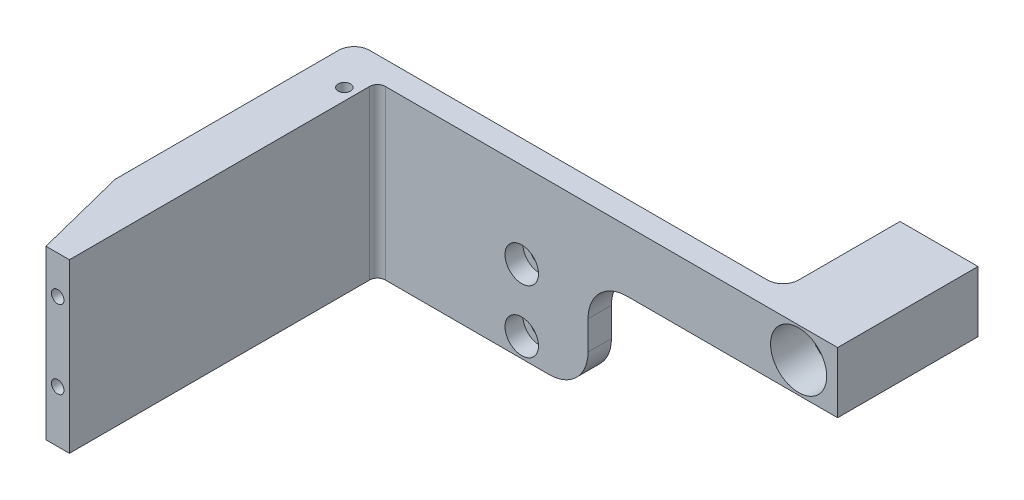
SolidWorks part; units mm, degrees
ref_plane "前视基准面" through (0, 0, 0) normal (0, 0, 1) x (1, 0, 0)
ref_plane "上视基准面" through (0, 0, 0) normal (0, 1, 0) x (1, 0, 0)
ref_plane "右视基准面" through (0, 0, 0) normal (1, 0, 0) x (0, 0, -1)
sketch "草图1" plane through (0, 0, 0) normal (0, 0, 1) x (1, 0, 0)
  line L1 (20, -5) -> (-20, -5)
  line L2 (20, -5) -> (20, 5)
  line L3 (20, 5) -> (-20, 5)
  line L4 (-20, -5) -> (-20, 5)
  line L5 (20, -5) -> (-20, 5) construction
  line L6 (20, 5) -> (-20, -5) construction
  point P0 (0, 0)
  dimension "D1" = 40
  dimension "D2" = 10
extrude "凸台-拉伸1" add sketch "草图1" along normal blind 3
sketch "草图2" plane through (0, 0, 3) normal (0, 0, 1) x (1, 0, 0)
  line L0 (-10, 5) -> (-10, -5)
  line L1 (20, 5) -> (-20, 5) construction
  line L2 (-20, -5) -> (20, -5) construction
  line L3 (-10, -5) -> (-7, -5)
  line L4 (-7, -5) -> (-7, 5)
  line L5 (-7, 5) -> (-10, 5)
  line L6 (-20, 5) -> (-20, -5) construction
  dimension "D1" = 3
  dimension "D2" = 10
extrude "凸台-拉伸2" add sketch "草图2" along normal blind 39.5
sketch "草图3" plane through (0, 5, 0) normal (0, 1, 0) x (1, 0, 0)
  line L0 (-20, -3) -> (-10, -42.5)
  line L1 (-10, -42.5) -> (-10, -30.2762)
  line L2 (-10, -42.5) -> (-10, -3) construction
  line L3 (-10, -30.2762) -> (-16.9054, -3)
  line L4 (-10, -3) -> (-20, -3) construction
  line L5 (-16.9054, -3) -> (-20, -3)
  dimension "D1" = 3
extrude "凸台-拉伸3" add sketch "草图3" against normal up to surface (10 mm away) up to face at (-4.25, -5, 12.125)
fillet "圆角1" radius 1 1 edges at (-7, 0, 3)
sketch "草图4" plane through (0, 5, 0) normal (0, 1, 0) x (1, 0, 0)
  line L0 (20, 0) -> (20, -3)
  line L1 (20, -3) -> (-20, -3)
  line L2 (20, -3) -> (-6, -3) construction
  line L3 (-20, -3) -> (-20, 0)
  line L4 (20, 0) -> (-20, 0) construction
  line L5 (-20, 0) -> (20, 0)
  dimension "D1" = 40
extrude "凸台-拉伸4" add sketch "草图4" along normal blind 10
mirror "镜向1" about plane through (0, 0, 0) normal (0, 1, 0) of "凸台-拉伸4"
hole_wizard "打孔尺寸(%根据)内六角圆柱头螺钉的类型1" positions "草图5" profile "草图6" counterbore size "M2" standard "GB"
sketch "草图5" plane through (0, 0, 3) normal (0, 0, 1) x (1, 0, 0)
  line L0 (20, -15) -> (20, 15) construction
  point P0 (11.5, 4)
  point P2 (11.5, -4)
  dimension "D1" = 8
  dimension "D2" = 4
  dimension "D3" = 8.5
sketch "草图6" plane through (11.5, 4, 3) normal (1, 0, 0) x (0, -1, 0)
  line L0 (0, 0) -> (0, 3.921)
  line L1 (0, 3.921) -> (1.2, 3.2)
  line L2 (1.2, 3.2) -> (1.2, 2.3)
  line L3 (1.2, 2.3) -> (2.15, 2.3)
  line L4 (2.15, 2.3) -> (2.15, 0)
  line L5 (2.15, 0) -> (0, 0)
  line L10 (0, 3.921) -> (-1.2, 3.2) construction
  line L11 (0, -6.35) -> (0, 107.95) construction
  dimension "孔直径" = 2.4
  dimension "孔深度" = 3.2
  dimension "柱形沉头孔直径" = 4.3
  dimension "柱形沉头孔深度" = 2.3
  dimension "导头角度" = 118
hole_wizard "M2 螺纹孔1" positions "草图7" profile "草图8" tap size "M2" standard "GB"
sketch "草图7" plane through (0, 0, 42.5) normal (0, 0, 1) x (1, 0, 0)
  point P0 (-8.5, 0.1457)
  point P3 (-8.5, 10.1457)
sketch "草图8" plane through (-8.5, 0.1457, 42.5) normal (1, 0, 0) x (0, -1, 0)
  line L0 (0, 0) -> (0, 5.6807)
  line L1 (0, 5.6807) -> (0.8, 5.2)
  line L2 (0.8, 5.2) -> (0.8, 0)
  line L5 (0.8, 0) -> (0, 0)
  line L10 (0, 5.6807) -> (-0.8, 5.2) construction
  line L11 (0, -6.35) -> (0, 107.95) construction
  dimension "螺纹孔钻头直径" = 1.6
  dimension "螺纹孔钻头深度" = 5.2
  dimension "导头角度" = 118
cosmetic thread "孔螺蚊线8" parameters "D1"=4, "D2"=2
sketch "草图13" plane through (0, 0, 0) normal (0, 0, -1) x (-1, 0, 0)
  line L0 (-20, -15) -> (-20, -6.5)
  line L1 (-20, -15) -> (-20, 15) construction
  line L2 (-20, -6.5) -> (20, -6.5)
  line L3 (20, 15) -> (20, -15) construction
  line L4 (20, -6.5) -> (20, -15)
  line L5 (20, -15) -> (-20, -15)
  dimension "D1" = 8.5
extrude "切除-拉伸2" cut sketch "草图13" against normal blind 10
sketch "草图14" plane through (20, 0, 0) normal (1, 0, 0) x (0, 0, -1)
  line L0 (0, 15) -> (-3, 15)
  line L1 (-3, 15) -> (-3, 7.2)
  line L2 (-3, -6.5) -> (-3, 15) construction
  line L3 (-3, 7.2) -> (0, 7.2)
  line L4 (0, -6.5) -> (0, 15) construction
  line L5 (0, 7.2) -> (0, 15)
  dimension "D1" = 7.8
sketch "草图16" plane through (0, 5, 0) normal (0, 1, 0) x (1, 0, 0)
  line L0 (-16.9054, -3) -> (-10, -30.2762)
  line L1 (-10, -30.2762) -> (-10, -3)
  line L2 (-10, -3) -> (-16.9054, -3)
extrude "凸台-拉伸7" add sketch "草图16" against normal blind 10
sketch "草图17" plane through (0, 0, 0) normal (0, 1, 0) x (1, 0, 0)
  line L0 (-22.2594, 3.7402) -> (-13, 3.7402)
  line L1 (-13, 3.7402) -> (-13, -39.3133)
  line L2 (-13, -39.3133) -> (-22.2594, -39.3133)
  line L3 (-22.2594, -39.3133) -> (-22.2594, 3.7402)
  line L4 (-7, -42.5) -> (-7, -4) construction
  dimension "D1" = 6
extrude "切除-拉伸3" cut sketch "草图17" against normal mid plane 40
extrude "凸台-拉伸8" add sketch "草图14" along normal blind 32
sketch "草图18" plane through (0, 0, 0) normal (0, 0, -1) x (-1, 0, 0)
  line L0 (-52, 7.2) -> (-42, 7.2)
  line L1 (-52, 7.2) -> (-20, 7.2) construction
  line L2 (-42, 7.2) -> (-42, 15)
  line L3 (-52, 15) -> (13, 15) construction
  line L4 (-42, 15) -> (-52, 15)
  line L5 (-52, 15) -> (-52, 7.2)
  dimension "D1" = 10
extrude "凸台-拉伸9" add sketch "草图18" along normal blind 15
sketch "草图19" plane through (0, 0, 3) normal (0, 0, 1) x (1, 0, 0)
  line L0 (52, 11.1) -> (47, 11.1) construction
  line L1 (52, 15) -> (52, 7.2) construction
  circle A0 centre (47, 11.1) radius 3.6
  dimension "D1" = 7.2
  dimension "D2" = 5
extrude "切除-拉伸4" cut sketch "草图19" against normal blind 5
hole_wizard "M4 螺纹孔1" positions "草图20" profile "草图21" tap size "M4" standard "GB" end condition through all
sketch "草图20" plane through (0, 0, -2) normal (0, 0, 1) x (1, 0, 0)
  point P0 (47, 11.1)
sketch "草图21" plane through (47, 11.1, -2) normal (1, 0, 0) x (0, -1, 0)
  line L0 (0, 0) -> (0, 13)
  line L1 (0, 13) -> (1.65, 13)
  line L2 (1.65, 13) -> (1.65, 0)
  line L5 (1.65, 0) -> (0, 0)
  line L11 (0, -6.35) -> (0, 107.95) construction
  dimension "通孔螺纹孔钻头直径" = 3.3
  dimension "通孔螺纹孔钻头深度" = 13
cosmetic thread "孔螺蚊线4" parameters "D2"=4
fillet "圆角2" radius 2 1 edges at (42, 11.1, 0)
sketch "草图22" plane through (0, 5, 0) normal (0, 1, 0) x (1, 0, 0)
  line L5 (-6, -3) -> (-13, -3)
  line L6 (-13, -3) -> (-13, -30.65)
  line L7 (-13, -30.65) -> (-10, -42.5)
  line L8 (-10, -42.5) -> (-7, -42.5)
  line L9 (-7, -42.5) -> (-7, -4)
  line L10 (-6, -3) -> (-13, -3)
  line L11 (-13, -3) -> (-13, -30.65)
  line L12 (-13, -30.65) -> (-10, -42.5)
  line L13 (-10, -42.5) -> (-7, -42.5)
  line L14 (-7, -42.5) -> (-7, -4)
  arc A1 (-6, -3) -> (-7, -4) centre (-6, -4) ccw
  arc A2 (-6, -3) -> (-7, -4) centre (-6, -4) ccw
  dimension "D1" = 0
extrude "凸台-拉伸10" add sketch "草图22" along normal up to surface (10 mm away) up to face at (28.9163, 15, -3.6551)
sketch "草图23" plane through (0, -5, 0) normal (0, -1, 0) x (1, 0, 0)
  line L5 (-10, 42.5) -> (-13, 30.65)
  line L6 (-13, 30.65) -> (-13, 3)
  line L7 (-13, 3) -> (-6, 3)
  line L8 (-7, 4) -> (-7, 42.5)
  line L9 (-7, 42.5) -> (-10, 42.5)
  line L10 (-10, 42.5) -> (-13, 30.65)
  line L11 (-13, 30.65) -> (-13, 3)
  line L12 (-13, 3) -> (-6, 3)
  line L13 (-7, 4) -> (-7, 42.5)
  line L14 (-7, 42.5) -> (-10, 42.5)
  arc A1 (-7, 4) -> (-6, 3) centre (-6, 4) ccw
  arc A2 (-7, 4) -> (-6, 3) centre (-6, 4) ccw
  dimension "D1" = 0
extrude "凸台-拉伸11" add sketch "草图23" along normal up to surface (1.5 mm away) up to face at (3.5, -6.5, 1.5)
hole_wizard "M2 螺纹孔2" positions "草图24" profile "草图25" tap size "M2" standard "GB"
sketch "草图24" plane through (0, 0, 42.5) normal (0, 0, 1) x (1, 0, 0)
  point P0 (-8.5, 10.1457)
sketch "草图25" plane through (-8.5, 10.1457, 42.5) normal (1, 0, 0) x (0, -1, 0)
  line L0 (0, 0) -> (0, 5.6807)
  line L1 (0, 5.6807) -> (0.8, 5.2)
  line L2 (0.8, 5.2) -> (0.8, 0)
  line L5 (0.8, 0) -> (0, 0)
  line L10 (0, 5.6807) -> (-0.8, 5.2) construction
  line L11 (0, -6.35) -> (0, 107.95) construction
  dimension "螺纹孔钻头直径" = 1.6
  dimension "螺纹孔钻头深度" = 5.2
  dimension "导头角度" = 118
cosmetic thread "孔螺蚊线9" parameters "D1"=4, "D2"=2
hole_wizard "M2 螺纹孔3" positions "草图26" profile "草图27" tap size "M2" standard "GB"
sketch "草图26" plane through (0, 15, 0) normal (0, 1, 0) x (1, 0, 0)
  point P0 (-8.5, -5.75)
sketch "草图27" plane through (-8.5, 15, 5.75) normal (1, 0, 0) x (0, 0, 1)
  line L0 (0, 0) -> (0, 5.6807)
  line L1 (0, 5.6807) -> (0.8, 5.2)
  line L2 (0.8, 5.2) -> (0.8, 0)
  line L5 (0.8, 0) -> (0, 0)
  line L10 (0, 5.6807) -> (-0.8, 5.2) construction
  line L11 (0, -6.35) -> (0, 107.95) construction
  dimension "螺纹孔钻头直径" = 1.6
  dimension "螺纹孔钻头深度" = 5.2
  dimension "导头角度" = 118
cosmetic thread "孔螺蚊线10" parameters "D1"=4, "D2"=2
hole_wizard "M2 螺纹孔4" positions "草图28" profile "草图29" tap size "M2" standard "GB"
sketch "草图28" plane through (0, -6.5, 0) normal (0, -1, 0) x (-1, 0, 0)
  point P0 (8.5, -5.75)
sketch "草图29" plane through (-8.5, -6.5, 5.75) normal (1, 0, 0) x (0, 0, -1)
  line L0 (0, 0) -> (0, 5.6807)
  line L1 (0, 5.6807) -> (0.8, 5.2)
  line L2 (0.8, 5.2) -> (0.8, 0)
  line L5 (0.8, 0) -> (0, 0)
  line L10 (0, 5.6807) -> (-0.8, 5.2) construction
  line L11 (0, -6.35) -> (0, 107.95) construction
  dimension "螺纹孔钻头直径" = 1.6
  dimension "螺纹孔钻头深度" = 5.2
  dimension "导头角度" = 118
cosmetic thread "孔螺蚊线11" parameters "D1"=4, "D2"=2
fillet "圆角3" radius 2 1 edges at (-13, 4.25, 0)
fillet "圆角4" radius 5 2 edges at (20, -6.5, 1.5) (20, 7.2, 1.5)
